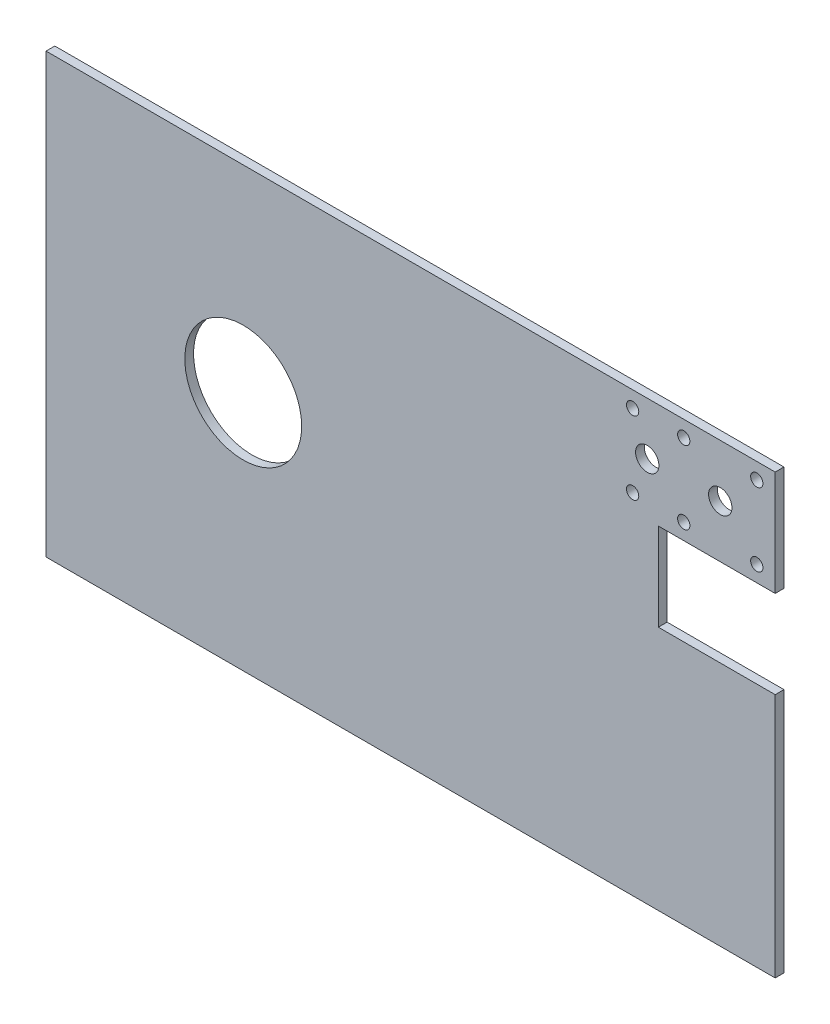
SolidWorks part; units mm, degrees
ref_plane "Front Plane" through (0, 0, 0) normal (0, 0, 1) x (1, 0, 0)
ref_plane "Top Plane" through (0, 0, 0) normal (0, 1, 0) x (1, 0, 0)
ref_plane "Right Plane" through (0, 0, 0) normal (1, 0, 0) x (0, 0, -1)
sketch "Sketch1" plane through (0, 0, 0) normal (0, 0, 1) x (1, 0, 0)
  line L1 (0, 0) -> (249.6, 0)
  line L2 (0, 0) -> (0, -150)
  line L3 (0, -150) -> (249.6, -150)
  line L4 (249.6, 0) -> (249.6, -150)
  dimension "D1" = 150
  dimension "D2" = 249.6
extrude "Boss-Extrude1" add sketch "Sketch1" along normal blind 3
sketch "Sketch2" plane through (0, 0, 3) normal (0, 0, 1) x (1, 0, 0)
  circle A0 centre (67.5, -67.5) radius 20
  circle A1 centre (67.5, -67.5) radius 62.5 construction
  dimension "D1" = 40
extrude "Cut-Extrude1" cut sketch "Sketch2" against normal through all
sketch "Sketch3" plane through (0, 0, 3) normal (0, 0, 1) x (1, 0, 0)
  line L0 (195.8, -36) -> (249.6, -36) construction
  line L1 (209.6, -36) -> (249.6, -36)
  line L2 (209.6, -36) -> (209.6, -66)
  line L3 (209.6, -66) -> (249.6, -66)
  line L4 (249.6, -36) -> (249.6, -66)
  line L5 (249.6, -150) -> (249.6, 0) construction
  dimension "D1" = 30
  dimension "D2" = 40
extrude "Cut-Extrude2" cut sketch "Sketch3" against normal blind 5
sketch "Sketch4" plane through (0, 0, 3) normal (0, 0, 1) x (1, 0, 0)
  circle A0 centre (200.8, -5.5) radius 2.1
  circle A1 centre (218.3, -5.5) radius 2.1
  circle A2 centre (205.8, -18) radius 4
  circle A3 centre (200.8, -30.5) radius 2.1
  circle A4 centre (218.3, -30.5) radius 2.1
  circle A5 centre (243.3, -5.5) radius 2.1
  circle A8 centre (243.3, -30.5) radius 2.1
  circle A9 centre (200.8, -5.5) radius 2.1 construction
  circle A10 centre (205.8, -18) radius 4 construction
  circle A11 centre (218.3, -5.5) radius 2.1 construction
  circle A12 centre (243.3, -30.5) radius 2.1 construction
  circle A13 centre (218.3, -30.5) radius 2.1 construction
  circle A14 centre (243.3, -5.5) radius 2.1 construction
  circle A16 centre (230.8, -18) radius 4
  circle A17 centre (230.8, -18) radius 4 construction
  circle A18 centre (200.8, -30.5) radius 2.1 construction
extrude "Cut-Extrude3" cut sketch "Sketch4" against normal through all
